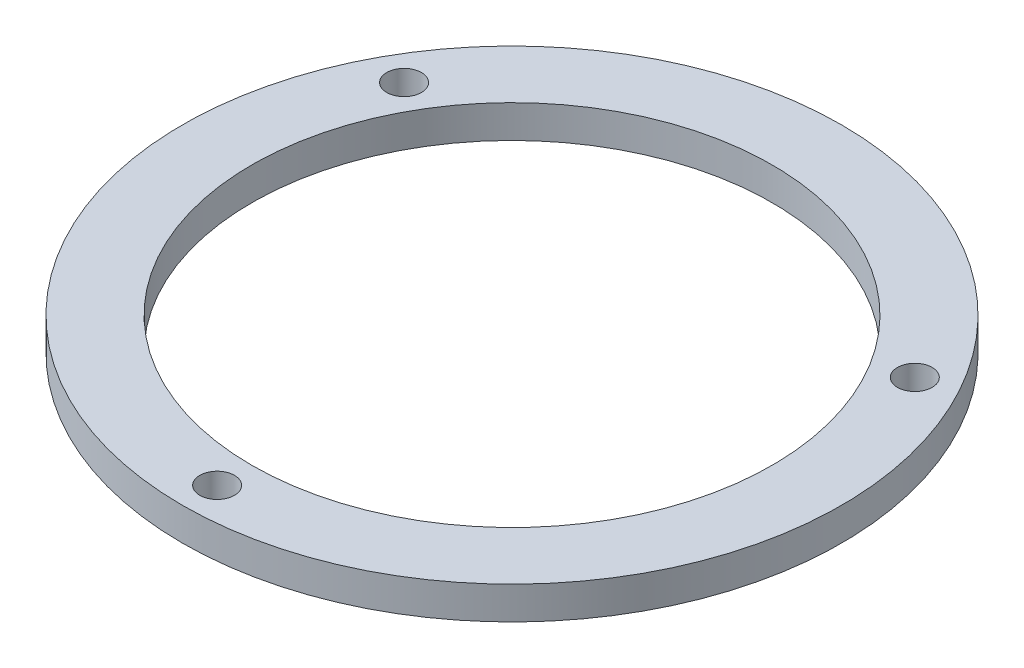
SolidWorks part; units mm, degrees
ref_plane "Front Plane" through (0, 0, 0) normal (0, 0, 1) x (1, 0, 0)
ref_plane "Top Plane" through (0, 0, 0) normal (0, 1, 0) x (1, 0, 0)
ref_plane "Right Plane" through (0, 0, 0) normal (1, 0, 0) x (0, 0, -1)
sketch "Sketch1" plane through (0, 0, 0) normal (0, 1, 0) x (1, 0, 0)
  line L0 (0, -47.6504) -> (0, -60.3504) construction
  circle A0 centre (0, 0) radius 60.3504
  circle A1 centre (0, 0) radius 47.6504
  circle A2 centre (0, -54.0004) radius 3.175
  circle A3 centre (-46.7657, 27.0002) radius 3.175
  circle A4 centre (46.7657, 27.0002) radius 3.175
  point P14 (0, 0)
  dimension "D1" = 120.7008
  dimension "D2" = 12.7
  dimension "D3" = 6.35
  dimension "D4" = 95.3008
  dimension "D5" = 3
extrude "Boss-Extrude1" add sketch "Sketch1" along normal blind 6 contours A2 | A4 | A3 | A0 | A1
